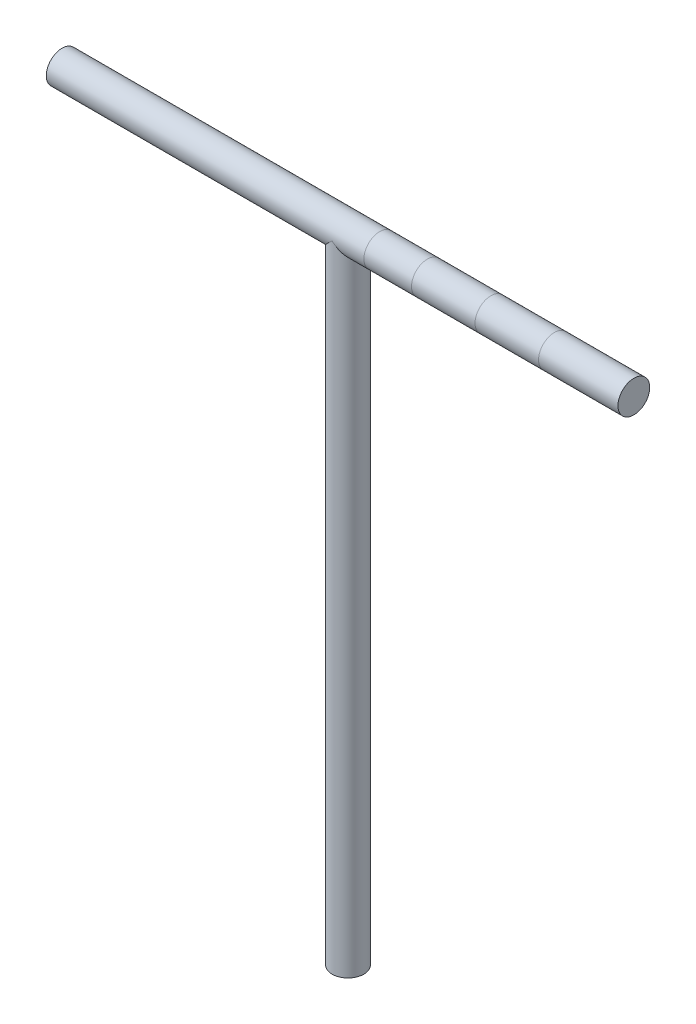
SolidWorks part; units mm, degrees
ref_plane "Front Plane" through (0, 0, 0) normal (0, 0, 1) x (1, 0, 0)
ref_plane "Top Plane" through (0, 0, 0) normal (0, 1, 0) x (1, 0, 0)
ref_plane "Right Plane" through (0, 0, 0) normal (1, 0, 0) x (0, 0, -1)
sketch "Sketch2" plane through (0, 0, 0) normal (1, 0, 0) x (0, 0, -1)
  circle A0 centre (0, 0) radius 5
extrude "Boss-Extrude6" add sketch "Sketch2" along normal mid plane 180 contours A0
ref_plane "Plane3" through (10, 0, 0) normal (1, 0, 0) x (0, 0, -1)
ref_plane "Plane4" through (25, 0, 0) normal (1, 0, 0) x (0, 0, -1)
ref_plane "Plane5" through (45, 0, 0) normal (1, 0, 0) x (0, 0, -1)
ref_plane "Plane6" through (65, 0, 0) normal (1, 0, 0) x (0, 0, -1)
split line "Split Line3"
sketch "Sketch8" plane through (0, 0, 0) normal (0, 1, 0) x (1, 0, 0)
  circle A0 centre (0, 0) radius 5
extrude "Boss-Extrude7" add sketch "Sketch8" against normal blind 200
